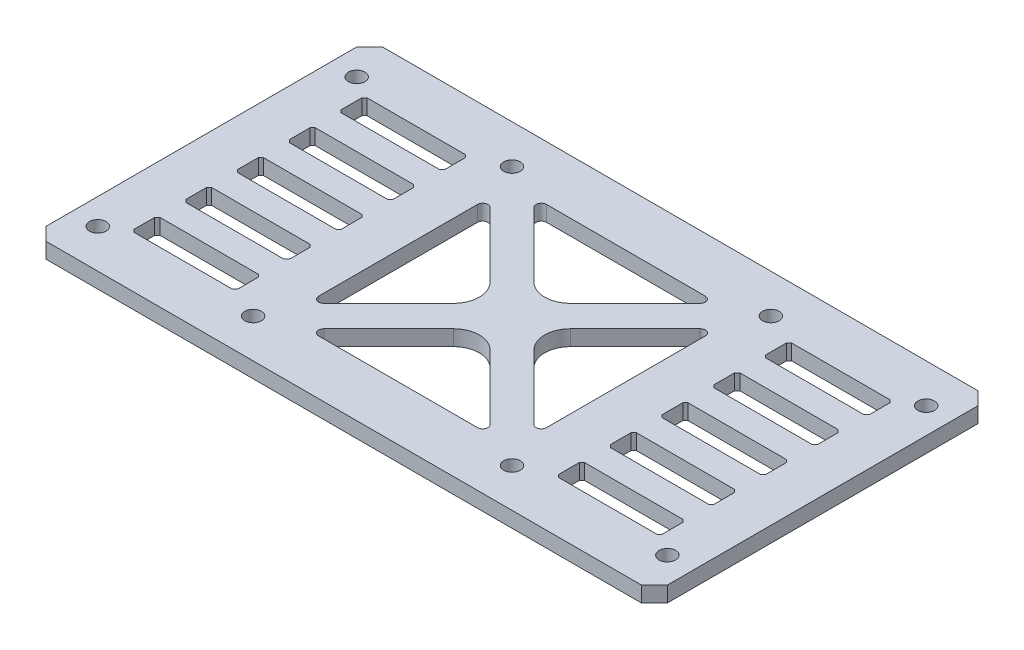
SolidWorks part; units mm, degrees
material "Thornel Mat VMA"
ref_plane "前视基准面" through (0, 0, 0) normal (0, 0, 1) x (1, 0, 0)
ref_plane "上视基准面" through (0, 0, 0) normal (0, 1, 0) x (1, 0, 0)
ref_plane "右视基准面" through (0, 0, 0) normal (1, 0, 0) x (0, 0, -1)
sketch "草图1" plane through (0, 0, 0) normal (0, 1, 0) x (1, 0, 0)
  line L0 (0, 0) -> (39.8628, 0) construction
  line L1 (-25, -25) -> (25, -25) construction
  line L2 (-25, -25) -> (-25, 25) construction
  line L3 (-25, 25) -> (25, 25) construction
  line L4 (25, -25) -> (25, 25) construction
  line L5 (-25, -25) -> (25, 25) construction
  line L6 (-25, 25) -> (25, -25) construction
  line L8 (-60, 32.5) -> (60, 32.5)
  line L9 (-60, 32.5) -> (-60, -32.5)
  line L10 (-60, -32.5) -> (60, -32.5)
  line L11 (60, 32.5) -> (60, -32.5)
  line L12 (-60, 32.5) -> (60, -32.5) construction
  line L13 (-60, -32.5) -> (60, 32.5) construction
  circle A0 centre (-25, 25) radius 1.6
  circle A1 centre (25, 25) radius 1.6
  circle A2 centre (25, -25) radius 1.6
  circle A3 centre (-25, -25) radius 1.6
  point P0 (0, 0)
  dimension "D3" = 3.2
  dimension "D4" = 3.2
  dimension "D1" = 50
  dimension "D2" = 50
  dimension "D5" = 65
  dimension "D6" = 120
extrude "凸台-拉伸1" add sketch "草图1" along normal blind 3
sketch "草图2" plane through (0, 3, 0) normal (0, 1, 0) x (1, 0, 0)
  line L0 (0, 32.5) -> (0, -32.5) construction
  line L1 (60, 32.5) -> (-60, 32.5) construction
  line L2 (-60, -32.5) -> (60, -32.5) construction
  line L3 (0, 0) -> (55, 0) construction
  line L4 (55, 25) -> (55, -25) construction
  circle A0 centre (55, 25) radius 1.6
  circle A1 centre (55, -25) radius 1.6
  circle A2 centre (-55, -25) radius 1.6
  circle A3 centre (-55, 25) radius 1.6
  dimension "D3" = 3.2
  dimension "D4" = 3.2
  dimension "D1" = 55
  dimension "D2" = 50
extrude "切除-拉伸1" cut sketch "草图2" against normal up to next
sketch "草图3" plane through (0, 3, 0) normal (0, 1, 0) x (1, 0, 0)
  line L0 (-25, 25) -> (-25, -25) construction
  line L1 (-25, -25) -> (0, 0) construction
  line L2 (0, 0) -> (-25, 25) construction
  line L3 (-22, 15.3431) -> (-22, -15.3431)
  line L4 (-20.2929, -16.0503) -> (-7.7782, -3.5355)
  line L5 (-7.7782, 3.5355) -> (-20.2929, 16.0503)
  line L6 (-22, -17.7574) -> (-4.2426, 0) construction
  line L7 (-4.2426, 0) -> (-22, 17.7574) construction
  line L8 (-22, 17.7574) -> (-22, -17.7574) construction
  line L9 (15.3431, 22) -> (-15.3431, 22)
  line L10 (3.5355, 7.7782) -> (16.0503, 20.2929)
  line L11 (-16.0503, 20.2929) -> (-3.5355, 7.7782)
  line L12 (22, -15.3431) -> (22, 15.3431)
  line L13 (7.7782, -3.5355) -> (20.2929, -16.0503)
  line L14 (20.2929, 16.0503) -> (7.7782, 3.5355)
  line L15 (-15.3431, -22) -> (15.3431, -22)
  line L16 (-3.5355, -7.7782) -> (-16.0503, -20.2929)
  line L17 (16.0503, -20.2929) -> (3.5355, -7.7782)
  arc A0 (-7.7782, -3.5355) -> (-7.7782, 3.5355) centre (-11.3137, 0) ccw
  arc A1 (-20.2929, -16.0503) -> (-22, -15.3431) centre (-21, -15.3431) cw
  arc A2 (-20.2929, 16.0503) -> (-22, 15.3431) centre (-21, 15.3431) ccw
  arc A3 (16.0503, 20.2929) -> (15.3431, 22) centre (15.3431, 21) ccw
  arc A4 (-3.5355, 7.7782) -> (3.5355, 7.7782) centre (0, 11.3137) ccw
  arc A5 (-16.0503, 20.2929) -> (-15.3431, 22) centre (-15.3431, 21) cw
  arc A6 (20.2929, -16.0503) -> (22, -15.3431) centre (21, -15.3431) ccw
  arc A7 (7.7782, 3.5355) -> (7.7782, -3.5355) centre (11.3137, 0) ccw
  arc A8 (20.2929, 16.0503) -> (22, 15.3431) centre (21, 15.3431) cw
  arc A9 (-16.0503, -20.2929) -> (-15.3431, -22) centre (-15.3431, -21) ccw
  arc A10 (3.5355, -7.7782) -> (-3.5355, -7.7782) centre (0, -11.3137) ccw
  arc A11 (16.0503, -20.2929) -> (15.3431, -22) centre (15.3431, -21) cw
  point P48 (0, 0)
  dimension "D2" = 5
  dimension "D3" = 1
  dimension "D1" = 3
  dimension "D4" = 4
extrude "切除-拉伸2" cut sketch "草图3" against normal up to next
sketch "草图4" plane through (0, 0, 0) normal (0, -1, 0) x (1, 0, 0)
  line L0 (60, 0) -> (22, 0) construction
  line L1 (60, 32.5) -> (60, -32.5) construction
  line L2 (22, -15.3431) -> (22, 15.3431) construction
  line L3 (50.5, -2.5) -> (51, -2)
  line L4 (50.5, -2.5) -> (31.5, -2.5)
  line L5 (51, -2) -> (51, 2)
  line L6 (50.5, 2.5) -> (31.5, 2.5)
  line L7 (31, -2) -> (31, 2)
  line L8 (51, -2.5) -> (31, 2.5) construction
  line L9 (51, 2.5) -> (31, -2.5) construction
  line L10 (31.5, -2.5) -> (31, -2)
  line L11 (51, 2) -> (50.5, 2.5)
  line L12 (31.5, 2.5) -> (31, 2)
  line L13 (50.5, 7.5) -> (31.5, 7.5)
  line L14 (50.5, 7.5) -> (51, 8)
  line L15 (51, 8) -> (51, 12)
  line L16 (51, 12) -> (50.5, 12.5)
  line L17 (50.5, 12.5) -> (31.5, 12.5)
  line L18 (31.5, 12.5) -> (31, 12)
  line L19 (31, 8) -> (31, 12)
  line L20 (31.5, 7.5) -> (31, 8)
  line L21 (50.5, 17.5) -> (31.5, 17.5)
  line L22 (50.5, 17.5) -> (51, 18)
  line L23 (51, 18) -> (51, 22)
  line L24 (51, 22) -> (50.5, 22.5)
  line L25 (50.5, 22.5) -> (31.5, 22.5)
  line L26 (31.5, 22.5) -> (31, 22)
  line L27 (31, 18) -> (31, 22)
  line L28 (31.5, 17.5) -> (31, 18)
  line L29 (31.5, -17.5) -> (31, -18)
  line L30 (31, -18) -> (31, -22)
  line L31 (31.5, -22.5) -> (31, -22)
  line L32 (50.5, -22.5) -> (31.5, -22.5)
  line L33 (51, -22) -> (50.5, -22.5)
  line L34 (51, -18) -> (51, -22)
  line L35 (50.5, -17.5) -> (51, -18)
  line L36 (50.5, -17.5) -> (31.5, -17.5)
  line L37 (31.5, -7.5) -> (31, -8)
  line L38 (31, -8) -> (31, -12)
  line L39 (31.5, -12.5) -> (31, -12)
  line L40 (50.5, -12.5) -> (31.5, -12.5)
  line L41 (51, -12) -> (50.5, -12.5)
  line L42 (51, -8) -> (51, -12)
  line L43 (50.5, -7.5) -> (51, -8)
  line L44 (50.5, -7.5) -> (31.5, -7.5)
  line L45 (0, 32.5) -> (0, -13.9632) construction
  line L46 (-60, 32.5) -> (60, 32.5) construction
  line L47 (-51, 2.5) -> (-31, -2.5) construction
  line L48 (-51, -2.5) -> (-31, 2.5) construction
  line L49 (-60, 0) -> (-22, 0) construction
  line L50 (-50.5, -7.5) -> (-31.5, -7.5)
  line L51 (-50.5, -7.5) -> (-51, -8)
  line L52 (-51, -8) -> (-51, -12)
  line L53 (-51, -12) -> (-50.5, -12.5)
  line L54 (-50.5, -12.5) -> (-31.5, -12.5)
  line L55 (-31.5, -12.5) -> (-31, -12)
  line L56 (-31, -8) -> (-31, -12)
  line L57 (-31.5, -7.5) -> (-31, -8)
  line L58 (-50.5, -17.5) -> (-31.5, -17.5)
  line L59 (-50.5, -17.5) -> (-51, -18)
  line L60 (-51, -18) -> (-51, -22)
  line L61 (-51, -22) -> (-50.5, -22.5)
  line L62 (-50.5, -22.5) -> (-31.5, -22.5)
  line L63 (-31.5, -22.5) -> (-31, -22)
  line L64 (-31, -18) -> (-31, -22)
  line L65 (-31.5, -17.5) -> (-31, -18)
  line L66 (-31.5, 17.5) -> (-31, 18)
  line L67 (-31, 18) -> (-31, 22)
  line L68 (-31.5, 22.5) -> (-31, 22)
  line L69 (-50.5, 22.5) -> (-31.5, 22.5)
  line L70 (-51, 22) -> (-50.5, 22.5)
  line L71 (-51, 18) -> (-51, 22)
  line L72 (-50.5, 17.5) -> (-51, 18)
  line L73 (-50.5, 17.5) -> (-31.5, 17.5)
  line L74 (-31.5, 7.5) -> (-31, 8)
  line L75 (-31, 8) -> (-31, 12)
  line L76 (-31.5, 12.5) -> (-31, 12)
  line L77 (-50.5, 12.5) -> (-31.5, 12.5)
  line L78 (-51, 12) -> (-50.5, 12.5)
  line L79 (-51, 8) -> (-51, 12)
  line L80 (-50.5, 7.5) -> (-51, 8)
  line L81 (-50.5, 7.5) -> (-31.5, 7.5)
  line L82 (-31.5, 2.5) -> (-31, 2)
  line L83 (-51, 2) -> (-50.5, 2.5)
  line L84 (-31.5, -2.5) -> (-31, -2)
  line L85 (-31, -2) -> (-31, 2)
  line L86 (-50.5, 2.5) -> (-31.5, 2.5)
  line L87 (-51, -2) -> (-51, 2)
  line L88 (-50.5, -2.5) -> (-31.5, -2.5)
  line L89 (-50.5, -2.5) -> (-51, -2)
  point P6 (41, 0)
  point P102 (-41, 0)
  dimension "D1" = 5
  dimension "D2" = 20
  dimension "D3" = 3
extrude "切除-拉伸3" cut sketch "草图4" against normal up to surface (3 mm away) up to face at (0, 3, 16.525)
chamfer "倒角1" distance 2.5 angle 45 4 edges at (60, 1.5, -32.5) (60, 1.5, 32.5) (-60, 1.5, 32.5) (-60, 1.5, -32.5)
